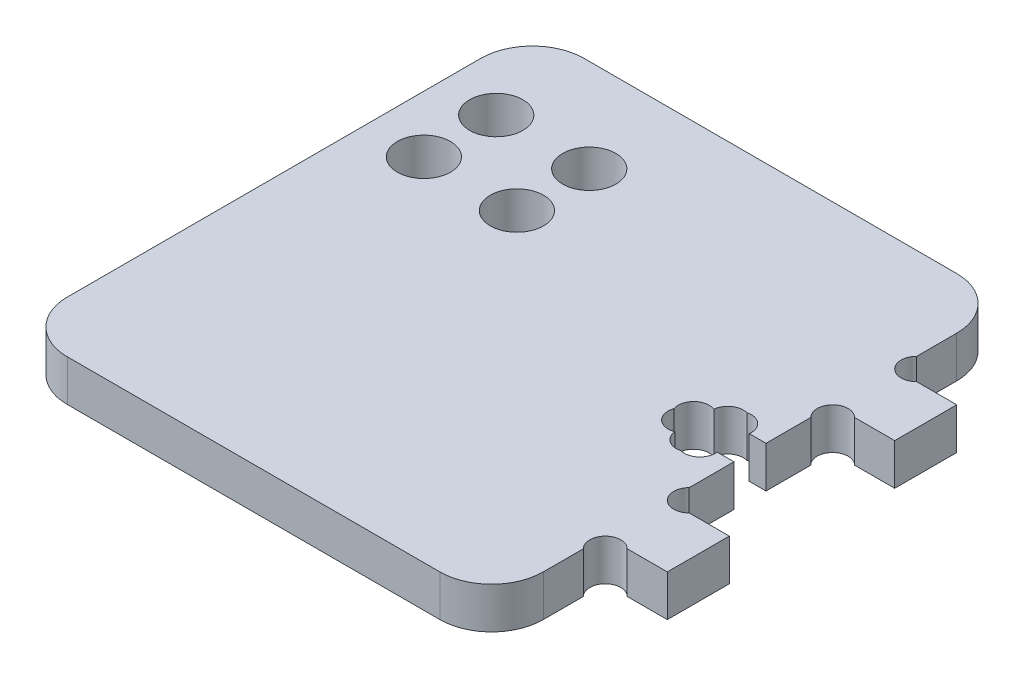
SolidWorks part; units mm, degrees
ref_plane "Alzado" through (0, 0, 0) normal (0, 0, 1) x (1, 0, 0)
ref_plane "Planta" through (0, 0, 0) normal (0, 1, 0) x (1, 0, 0)
ref_plane "Vista lateral" through (0, 0, 0) normal (1, 0, 0) x (0, 0, -1)
sketch "Croquis1" plane through (0, 0, 0) normal (0, 1, 0) x (1, 0, 0)
  line L0 (26.025, 14) -> (26.025, -14) construction
  line L1 (-18.025, -25) -> (18.025, -25)
  line L2 (-23.025, -20) -> (-23.025, 20)
  line L3 (-18.025, 25) -> (18.025, 25)
  line L4 (23.025, -20) -> (23.025, -14)
  line L5 (-23.025, -25) -> (23.025, 25) construction
  line L6 (-23.025, 25) -> (23.025, -25) construction
  line L7 (23.025, 14) -> (29.025, 14)
  line L8 (23.025, -8) -> (23.025, -1.55)
  line L9 (23.025, 8) -> (29.025, 8)
  line L10 (29.025, 14) -> (29.025, 8)
  line L11 (23.025, -8) -> (29.025, -8)
  line L12 (29.025, 11) -> (8.3263, 11) construction
  line L13 (23.025, -14) -> (29.025, -14)
  line L14 (29.025, -8) -> (29.025, -14)
  line L15 (0, 0) -> (26.025, 0) construction
  line L16 (23.025, 14) -> (23.025, 20)
  line L17 (20.975, -1.55) -> (20.975, -2.8)
  line L18 (18.075, 2.8) -> (20.975, 2.8)
  line L19 (18.075, 2.8) -> (18.075, 1.55)
  line L20 (18.075, -2.8) -> (20.975, -2.8)
  line L21 (20.975, 2.8) -> (20.975, 1.55)
  line L22 (16.025, 1.55) -> (18.075, 1.55)
  line L23 (16.025, 1.55) -> (16.025, -1.55)
  line L24 (16.025, -1.55) -> (18.075, -1.55)
  line L25 (23.025, 1.55) -> (23.025, 8)
  line L26 (20.975, 1.55) -> (23.025, 1.55)
  line L27 (18.075, -1.55) -> (18.075, -2.8)
  line L28 (20.975, -1.55) -> (23.025, -1.55)
  line L29 (16.025, 0) -> (0, 0) construction
  line L30 (19.525, 2.8) -> (19.525, -2.8) construction
  line L31 (19.525, 0) -> (16.025, 0) construction
  arc A0 (-18.025, -25) -> (-23.025, -20) centre (-18.025, -20) cw
  arc A1 (18.025, -25) -> (23.025, -20) centre (18.025, -20) ccw
  arc A2 (18.025, 25) -> (23.025, 20) centre (18.025, 20) cw
  arc A3 (-23.025, 20) -> (-18.025, 25) centre (-18.025, 20) cw
  point P0 (0, 0)
  dimension "D3" = 5
  dimension "D4" = 6
  dimension "D1" = 50
  dimension "D2" = 46.05
  dimension "D5" = 6
  dimension "D6" = 14
  dimension "D7" = 3.1
  dimension "D8" = 5.6
  dimension "D9" = 2.9
  dimension "D10" = 7
  dimension "D11" = 3.5
extrude "Saliente-Extruir1" add sketch "Croquis1" along normal blind 4
sketch "Croquis4" plane through (0, 0, 0) normal (0, 1, 0) x (1, 0, 0)
  line L1 (8.4, 26.5) -> (14.55, 26.5)
  line L2 (8.4, 26.5) -> (8.4, -26.5)
  line L3 (8.4, -26.5) -> (14.55, -26.5)
  line L4 (14.55, 26.5) -> (14.55, -26.5)
  line L6 (11.475, 26.5) -> (11.475, -26.5) construction
  line L7 (23.025, -20) -> (23.025, -14) construction
  line L8 (18.025, 25) -> (-18.025, 25) construction
  line L9 (-18.025, -25) -> (18.025, -25) construction
  dimension "D1" = 6.15
  dimension "D2" = 11.55
  dimension "D3" = 1.5
  dimension "D4" = 1.5
sketch "Croquis9" plane through (0, 4, 0) normal (0, 1, 0) x (1, 0, 0)
  line L24 (-18.025, -25) -> (18.025, -25)
  line L25 (23.025, -20) -> (23.025, -14)
  line L26 (23.025, -14) -> (29.025, -14)
  line L27 (29.025, -14) -> (29.025, -8)
  line L28 (29.025, -8) -> (23.025, -8)
  line L29 (23.025, -8) -> (23.025, -1.55)
  line L30 (23.025, -1.55) -> (20.975, -1.55)
  line L31 (20.975, -1.55) -> (20.975, -2.8)
  line L32 (20.975, -2.8) -> (18.075, -2.8)
  line L33 (18.075, -2.8) -> (18.075, -1.55)
  line L34 (18.075, -1.55) -> (16.025, -1.55)
  line L35 (16.025, -1.55) -> (16.025, 1.55)
  line L36 (16.025, 1.55) -> (18.075, 1.55)
  line L37 (18.075, 1.55) -> (18.075, 2.8)
  line L38 (18.075, 2.8) -> (20.975, 2.8)
  line L39 (20.975, 2.8) -> (20.975, 1.55)
  line L40 (20.975, 1.55) -> (23.025, 1.55)
  line L41 (23.025, 1.55) -> (23.025, 8)
  line L42 (23.025, 8) -> (29.025, 8)
  line L43 (29.025, 8) -> (29.025, 14)
  line L44 (29.025, 14) -> (23.025, 14)
  line L45 (23.025, 14) -> (23.025, 20)
  line L46 (18.025, 25) -> (-18.025, 25)
  line L47 (-23.025, 20) -> (-23.025, -20)
  line L48 (-18.025, -25) -> (18.025, -25)
  line L49 (23.025, -20) -> (23.025, -14)
  line L50 (23.025, -14) -> (29.025, -14)
  line L51 (29.025, -14) -> (29.025, -8)
  line L52 (29.025, -8) -> (23.025, -8)
  line L53 (23.025, -8) -> (23.025, -1.55)
  line L54 (23.025, -1.55) -> (20.975, -1.55)
  line L55 (20.975, -1.55) -> (20.975, -2.8)
  line L56 (20.975, -2.8) -> (18.075, -2.8)
  line L57 (18.075, -2.8) -> (18.075, -1.55)
  line L58 (18.075, -1.55) -> (16.025, -1.55)
  line L59 (16.025, -1.55) -> (16.025, 1.55)
  line L60 (16.025, 1.55) -> (18.075, 1.55)
  line L61 (18.075, 1.55) -> (18.075, 2.8)
  line L62 (18.075, 2.8) -> (20.975, 2.8)
  line L63 (20.975, 2.8) -> (20.975, 1.55)
  line L64 (20.975, 1.55) -> (23.025, 1.55)
  line L65 (23.025, 1.55) -> (23.025, 8)
  line L66 (23.025, 8) -> (29.025, 8)
  line L67 (29.025, 8) -> (29.025, 14)
  line L68 (29.025, 14) -> (23.025, 14)
  line L69 (23.025, 14) -> (23.025, 20)
  line L70 (18.025, 25) -> (-18.025, 25)
  line L71 (-23.025, 20) -> (-23.025, -20)
  arc A4 (-23.025, -20) -> (-18.025, -25) centre (-18.025, -20) ccw
  arc A5 (18.025, -25) -> (23.025, -20) centre (18.025, -20) ccw
  arc A6 (23.025, 20) -> (18.025, 25) centre (18.025, 20) ccw
  arc A7 (-18.025, 25) -> (-23.025, 20) centre (-18.025, 20) ccw
  arc A8 (-23.025, -20) -> (-18.025, -25) centre (-18.025, -20) ccw
  arc A9 (18.025, -25) -> (23.025, -20) centre (18.025, -20) ccw
  arc A10 (23.025, 20) -> (18.025, 25) centre (18.025, 20) ccw
  arc A11 (-18.025, 25) -> (-23.025, 20) centre (-18.025, 20) ccw
  dimension "D1" = 0
sketch "Croquis6" plane through (0, 4, 0) normal (0, 1, 0) x (1, 0, 0)
  line L0 (16.025, 1.55) -> (18.075, 1.55) construction
  line L1 (16.025, -1.55) -> (16.025, 1.55) construction
  line L2 (18.075, -1.55) -> (16.025, -1.55) construction
  line L3 (16.025, 1.55) -> (17.525, 0.05)
  line L4 (16.025, -1.55) -> (17.525, -0.05)
  line L5 (18.075, 2.8) -> (20.975, 2.8) construction
  line L6 (18.075, 1.55) -> (18.075, 2.8) construction
  line L7 (18.075, 2.8) -> (19.575, 1.3)
  line L8 (20.975, 2.8) -> (20.975, 1.55) construction
  line L9 (20.975, 2.8) -> (19.475, 1.3)
  line L10 (18.075, -2.8) -> (18.075, -1.55) construction
  line L11 (20.975, -2.8) -> (18.075, -2.8) construction
  line L12 (18.075, -2.8) -> (19.575, -1.3)
  line L13 (20.975, -1.55) -> (20.975, -2.8) construction
  line L14 (20.975, -2.8) -> (19.475, -1.3)
  circle A0 centre (17.525, 0.05) radius 1.5
  circle A1 centre (17.525, -0.05) radius 1.5
  circle A2 centre (19.575, -1.3) radius 1.5
  circle A3 centre (19.475, -1.3) radius 1.5
  circle A4 centre (19.475, 1.3) radius 1.5
  circle A5 centre (19.575, 1.3) radius 1.5
  dimension "D1" = 3
sketch "Croquis7" plane through (0, 4, 0) normal (0, 1, 0) x (1, 0, 0)
  line L0 (16.025, 1.55) -> (17.525, 0.05) construction
  line L1 (16.025, -1.55) -> (17.525, -0.05) construction
  line L2 (18.075, -2.8) -> (19.575, -1.3) construction
  line L3 (20.975, -2.8) -> (19.475, -1.3) construction
  line L4 (20.975, 2.8) -> (19.475, 1.3) construction
  line L5 (18.075, 2.8) -> (19.575, 1.3) construction
  line L11 (21.4023, 1.55) -> (23.025, 1.55)
  line L12 (23.025, 1.55) -> (23.025, -1.55)
  line L13 (23.025, -1.55) -> (21.4023, -1.55)
  arc A0 (17.6425, 1.8822) -> (15.6677, 0) centre (17.0857, 0.4893) ccw
  arc A1 (15.6677, 0) -> (17.6425, -1.8822) centre (17.0857, -0.4893) ccw
  arc A2 (17.6425, -1.8822) -> (19.525, -3.1879) centre (19.1357, -1.7393) ccw
  arc A3 (19.525, -3.1879) -> (21.4023, -1.55) centre (19.9143, -1.7393) ccw
  arc A4 (21.4023, 1.55) -> (19.525, 3.1879) centre (19.9143, 1.7393) ccw
  arc A5 (19.525, 3.1879) -> (17.6425, 1.8822) centre (19.1357, 1.7393) ccw
  dimension "D1" = 3
extrude "Cortar-Extruir4" cut sketch "Croquis7" against normal through all
sketch "Croquis10" plane through (0, 4, 0) normal (0, 1, 0) x (1, 0, 0)
  line L0 (0, 0) -> (23.8324, 0) construction
  line L1 (29.025, 14) -> (23.025, 14) construction
  line L2 (23.025, 14) -> (23.025, 20) construction
  line L3 (23.025, 8) -> (29.025, 8) construction
  line L4 (23.025, 1.55) -> (23.025, 8) construction
  line L5 (23.025, 14) -> (24.525, 15.5) construction
  line L7 (23.025, 8) -> (24.525, 6.5) construction
  circle A0 centre (24.525, 15.5) radius 1.5 construction
  circle A1 centre (24.525, 6.5) radius 1.5 construction
  circle A2 centre (24.0857, 15.0607) radius 1.5
  circle A3 centre (24.0857, 6.9393) radius 1.5
  circle A4 centre (24.0857, -15.0607) radius 1.5
  circle A5 centre (24.0857, -6.9393) radius 1.5
  dimension "D1" = 3
extrude "Cortar-Extruir5" cut sketch "Croquis10" against normal through all
sketch "Croquis11" plane through (0, 4, 0) normal (0, 1, 0) x (1, 0, 0)
  line L0 (-16.775, 9) -> (-18.275, 9) construction
  line L1 (-16.775, 7) -> (-18.275, 7)
  line L2 (-16.775, 11) -> (-18.275, 11)
  line L3 (-16.775, 16) -> (-18.275, 16) construction
  line L4 (-16.775, 14) -> (-18.275, 14)
  line L5 (-16.775, 18) -> (-18.275, 18)
  line L6 (-9.275, 9) -> (-7.775, 9) construction
  line L7 (-23.025, 20) -> (-3.025, 20) construction
  line L8 (-23.025, 20) -> (-23.025, 5) construction
  line L9 (-23.025, 5) -> (-3.025, 5) construction
  line L10 (-3.025, 20) -> (-3.025, 5) construction
  line L11 (-17.525, 16) -> (-17.525, 9) construction
  line L12 (-17.525, 12.5) -> (-13.025, 12.5) construction
  line L13 (-13.025, 20) -> (-13.025, 5) construction
  line L14 (-9.275, 7) -> (-7.775, 7)
  line L15 (-9.275, 11) -> (-7.775, 11)
  line L16 (-9.275, 16) -> (-7.775, 16) construction
  line L17 (-9.275, 14) -> (-7.775, 14)
  line L18 (-9.275, 18) -> (-7.775, 18)
  line L19 (18.025, 25) -> (-18.025, 25) construction
  line L21 (-23.025, 20) -> (-23.025, -20) construction
  arc A0 (-16.775, 7) -> (-16.775, 11) centre (-16.775, 9) ccw
  arc A1 (-18.275, 11) -> (-18.275, 7) centre (-18.275, 9) ccw
  arc A2 (-16.775, 14) -> (-16.775, 18) centre (-16.775, 16) ccw
  arc A3 (-18.275, 18) -> (-18.275, 14) centre (-18.275, 16) ccw
  arc A4 (-9.275, 7) -> (-9.275, 11) centre (-9.275, 9) cw
  arc A5 (-7.775, 11) -> (-7.775, 7) centre (-7.775, 9) cw
  arc A6 (-9.275, 14) -> (-9.275, 18) centre (-9.275, 16) cw
  arc A7 (-7.775, 18) -> (-7.775, 14) centre (-7.775, 16) cw
  point P2 (-17.525, 9)
  point P17 (-17.525, 16)
  point P26 (-8.525, 9)
  point P33 (-8.525, 16)
  dimension "D3" = 2
  dimension "D1" = 11
  dimension "D2" = 1.5
  dimension "D4" = 20
  dimension "D5" = 15
  dimension "D6" = 9
  dimension "D7" = 5
sketch "Croquis12" plane through (0, 4, 0) normal (0, 1, 0) x (1, 0, 0)
  circle A0 centre (-17.525, 16) radius 2.575
  circle A1 centre (-8.525, 16) radius 2.575
  circle A2 centre (-8.525, 9) radius 2.575
  circle A3 centre (-17.525, 9) radius 2.575
  dimension "D1" = 5.15
extrude "Cortar-Extruir6" cut sketch "Croquis12" against normal through all
